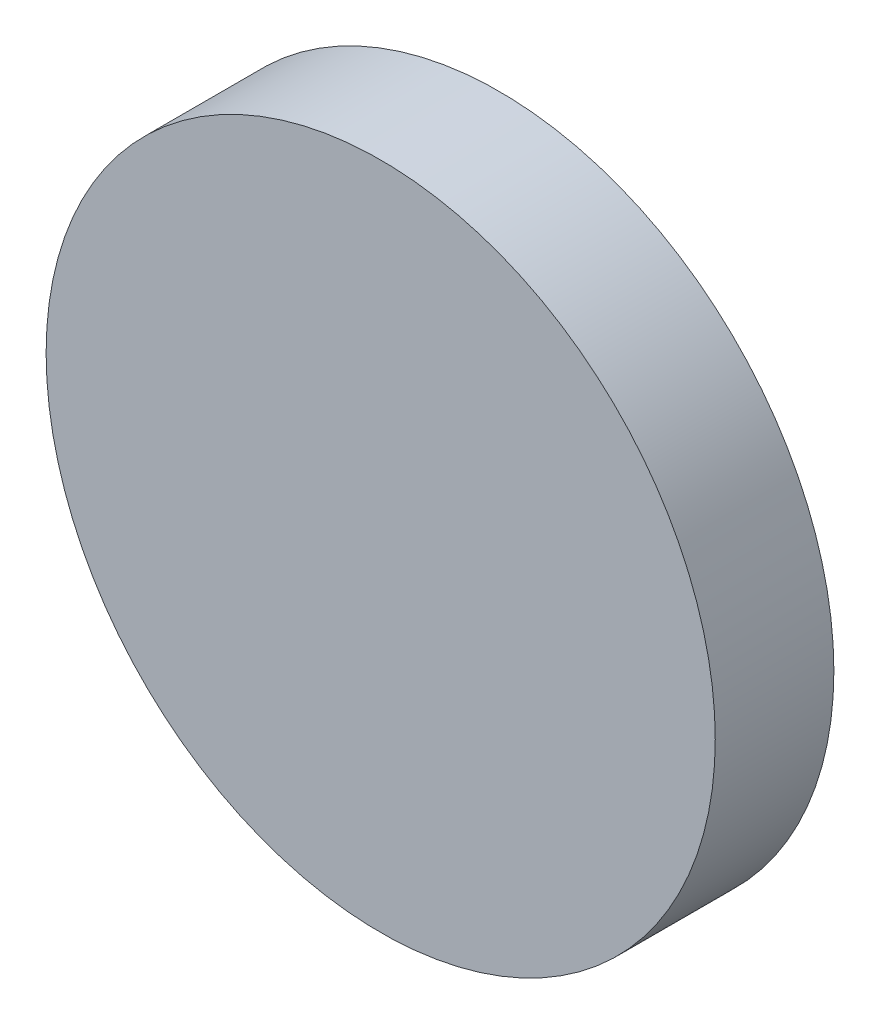
SolidWorks part; units mm, degrees
ref_plane "Front" through (0, 0, 0) normal (0, 0, 1) x (1, 0, 0)
ref_plane "Top" through (0, 0, 0) normal (0, 1, 0) x (1, 0, 0)
ref_plane "Right" through (0, 0, 0) normal (1, 0, 0) x (0, 0, -1)
sketch "Sketch3" plane through (0, 0, 0) normal (0, 0, 1) x (1, 0, 0)
  circle A0 centre (0, 0) radius 11
  dimension "D1" = 22
extrude "Boss-Extrude1" add sketch "Sketch3" along normal blind 3.9 contours A0
